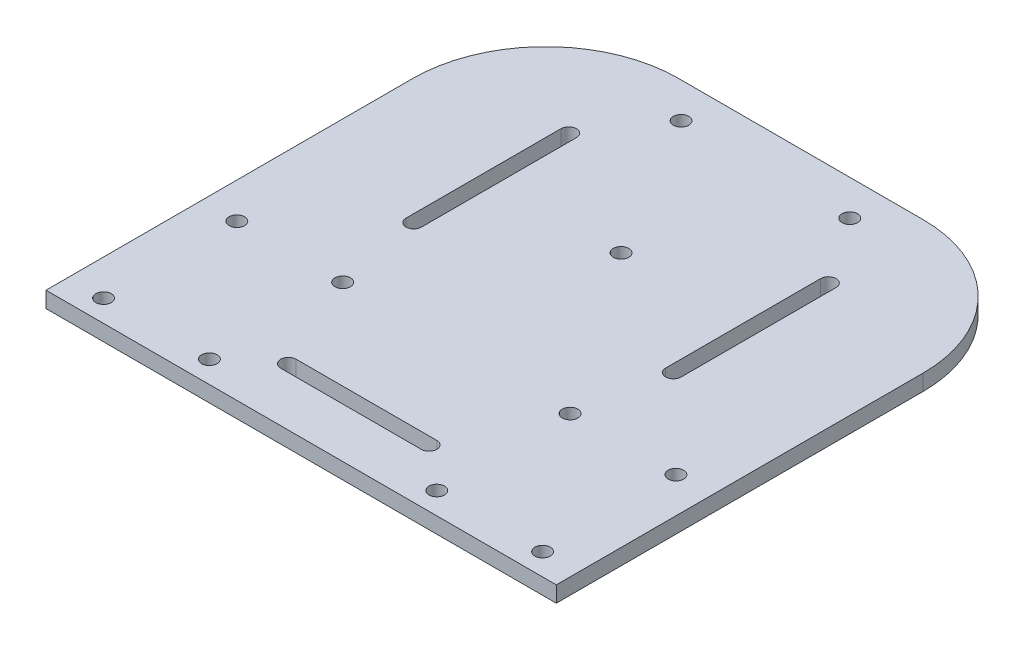
SolidWorks part; units mm, degrees
ref_plane "前视基准面" through (0, 0, 0) normal (0, 0, 1) x (1, 0, 0)
ref_plane "上视基准面" through (0, 0, 0) normal (0, 1, 0) x (1, 0, 0)
ref_plane "右视基准面" through (0, 0, 0) normal (1, 0, 0) x (0, 0, -1)
sketch "草图6" plane through (0, 0, 0) normal (0, 1, 0) x (1, 0, 0)
  line L0 (0, 0) -> (0, 140)
  line L1 (0, 0) -> (190, 0)
  line L2 (0, 140) -> (0, 0)
  line L3 (0, 140) -> (190, 140)
  line L4 (0, 0) -> (190, 0)
  line L5 (190, 140) -> (190, 0)
  line L6 (-905, 70) -> (49095, 70) construction
  line L7 (95, -930) -> (95, 49070) construction
  line L13 (-956.7369, 63.9433) -> (49043.2631, 63.9433) construction
  line L14 (37.3725, 140) -> (152.6275, 140)
  line L19 (37.3725, 140) -> (37.3725, 27.1433)
  line L20 (152.6275, 140) -> (152.6275, 27.1433)
  line L21 (37.3725, 27.1433) -> (152.6275, 27.1433)
  line L30 (95, 132) -> (63.2188, 132) construction
  line L31 (77.7, 132) -> (112.3, 132)
  line L32 (37.3725, 67.1433) -> (37.3725, 27.1433)
  line L33 (37.3725, 67.1433) -> (77.3725, 67.1433)
  line L34 (37.3725, 27.1433) -> (77.3725, 27.1433)
  line L35 (77.3725, 67.1433) -> (77.3725, 27.1433)
  line L36 (-964.7869, 47.1433) -> (49035.2131, 47.1433) construction
  line L37 (144.8209, -937.8067) -> (144.8209, 49062.1933) construction
  line L38 (132.6275, -932.8567) -> (132.6275, 49067.1433) construction
  line L39 (57.3725, -932.8567) -> (57.3725, 49067.1433) construction
  line L40 (45.1791, -938.4094) -> (45.1791, 49061.5906) construction
  line L41 (65.6791, -938.4094) -> (65.6791, 49061.5906) construction
  line L42 (71.1725, -937.8067) -> (71.1725, 49062.1933) construction
  line L43 (1146.7369, 63.9433) -> (-48853.2631, 63.9433) construction
  line L44 (118.8275, -937.8067) -> (118.8275, 49062.1933) construction
  line L45 (124.3209, -937.8067) -> (124.3209, 49062.1933) construction
  line L46 (1154.7869, 47.1433) -> (-48845.2131, 47.1433) construction
  line L47 (152.6275, 67.1433) -> (112.6275, 67.1433)
  line L48 (112.6275, 67.1433) -> (112.6275, 27.1433)
  line L49 (152.6275, 27.1433) -> (112.6275, 27.1433)
  line L50 (152.6275, 67.1433) -> (152.6275, 27.1433)
  line L51 (-909.5132, 40.1433) -> (49090.4868, 40.1433) construction
  line L52 (79.1225, 40.1433) -> (110.8775, 40.1433) construction
  line L53 (79.1225, 41.8933) -> (110.8775, 41.8933)
  line L54 (79.1225, 38.3933) -> (110.8775, 38.3933)
  line L55 (77.7, -868) -> (77.7, 49132) construction
  line L56 (77.3725, -960.0173) -> (77.3725, 49039.9827) construction
  line L57 (65.6791, 81.8933) -> (65.6791, 116.8933) construction
  line L58 (63.9291, 81.8933) -> (63.9291, 116.8933)
  line L59 (67.4291, 81.8933) -> (67.4291, 116.8933)
  line L60 (124.3209, 81.8933) -> (124.3209, 116.8933) construction
  line L61 (126.0709, 81.8933) -> (126.0709, 116.8933)
  line L62 (122.5709, 81.8933) -> (122.5709, 116.8933)
  line L63 (-934.3209, 99.3933) -> (49065.6791, 99.3933) construction
  circle A8 centre (75.95, 132) radius 1.75
  circle A9 centre (114.05, 132) radius 1.75
  circle A10 centre (69.3225, 62.1933) radius 1.75
  circle A11 centre (45.4225, 62.1933) radius 1.75
  circle A12 centre (69.3225, 32.0933) radius 1.75
  circle A13 centre (45.4225, 32.0933) radius 1.75
  circle A14 centre (120.6775, 32.0933) radius 1.75
  circle A15 centre (144.5775, 32.0933) radius 1.75
  circle A16 centre (144.5775, 62.1933) radius 1.75
  circle A17 centre (120.6775, 62.1933) radius 1.75
  arc A18 (79.1225, 41.8933) -> (79.1225, 38.3933) centre (79.1225, 40.1433) ccw
  arc A19 (110.8775, 38.3933) -> (110.8775, 41.8933) centre (110.8775, 40.1433) ccw
  arc A20 (63.9291, 81.8933) -> (67.4291, 81.8933) centre (65.6791, 81.8933) ccw
  arc A21 (67.4291, 116.8933) -> (63.9291, 116.8933) centre (65.6791, 116.8933) ccw
  arc A22 (126.0709, 81.8933) -> (122.5709, 81.8933) centre (124.3209, 81.8933) cw
  arc A23 (122.5709, 116.8933) -> (126.0709, 116.8933) centre (124.3209, 116.8933) cw
  circle A24 centre (95, 99.3933) radius 1.75
  point P5 (95, 27.1433)
  point P12 (95, 70)
  point P17 (95, 70)
  point P21 (37.3725, 47.1433)
  point P28 (57.3725, 67.1433)
  point P56 (95, 132)
  point P79 (95, 40.1433)
  point P89 (77.3725, 40.1433)
  point P91 (65.6791, 99.3933)
  point P96 (65.6791, 80.1433)
  point P99 (124.3209, 99.3933)
  dimension "D1" = 0
  dimension "D3" = 20.5
  dimension "D5" = 140
  dimension "D7" = 8
  dimension "D9" = 3.2
  dimension "D10" = 3.5
  dimension "D11" = 40
  dimension "D13" = 0
  dimension "D14" = 30.1
  dimension "D15" = 3.5
  dimension "D2" = 13
  dimension "D16" = 58.6418
  dimension "D4" = 6.2
  dimension "D6" = 190
  dimension "D8" = 34.6
  dimension "D12" = 13
  dimension "D17" = 17.5
  dimension "D18" = 59.25
extrude "凸台-拉伸1" add sketch "草图6" along normal blind 3.6
fillet "圆角2" radius 30 1 edges at (37.3725, 1.8, -140)
fillet "圆角3" radius 30 1 edges at (152.6275, 1.8, -140)
